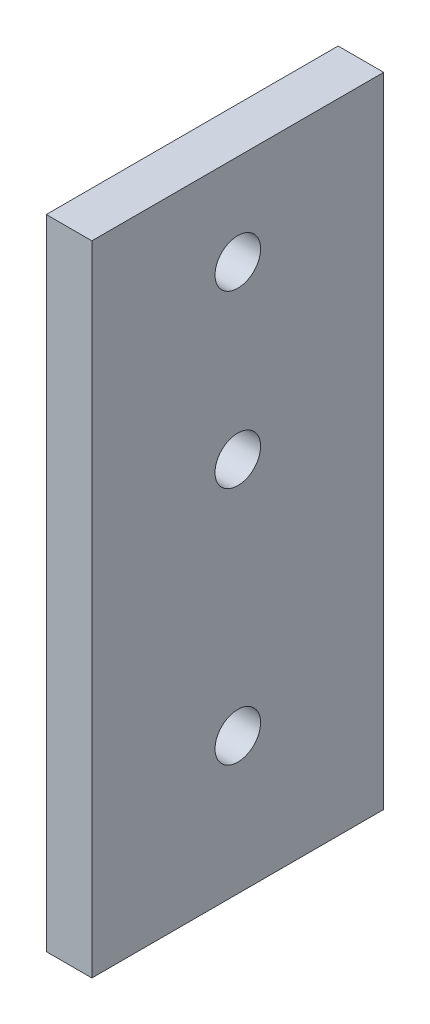
SolidWorks part; units mm, degrees
ref_plane "Front Plane" through (0, 0, 0) normal (0, 0, 1) x (1, 0, 0)
ref_plane "Top Plane" through (0, 0, 0) normal (0, 1, 0) x (1, 0, 0)
ref_plane "Right Plane" through (0, 0, 0) normal (1, 0, 0) x (0, 0, -1)
sketch "Sketch1" plane through (0, 0, 0) normal (1, 0, 0) x (0, 0, -1)
  line L1 (0, 0) -> (40.64, 0)
  line L2 (0, 0) -> (0, 88.9)
  line L3 (0, 88.9) -> (40.64, 88.9)
  line L4 (40.64, 0) -> (40.64, 88.9)
  dimension "D1" = 40.64
  dimension "D2" = 88.9
extrude "Boss-Extrude1" add sketch "Sketch1" along normal blind 6.35
sketch "Sketch3" plane through (6.35, 0, 0) normal (1, 0, 0) x (0, 0, -1)
  line L1 (0, 88.9) -> (0, 0) construction
  line L2 (40.64, 88.9) -> (0, 88.9) construction
  circle A0 centre (20.32, 19.05) radius 3.175
  circle A1 centre (20.32, 52.3875) radius 3.175
  circle A2 centre (20.32, 76.2) radius 3.175
  dimension "D1" = 33.3375
  dimension "D2" = 23.8125
  dimension "D5" = 20.32
  dimension "D6" = 6.35
  dimension "D3" = 12.7
extrude "Cut-Extrude1" cut sketch "Sketch3" against normal blind 6.35
